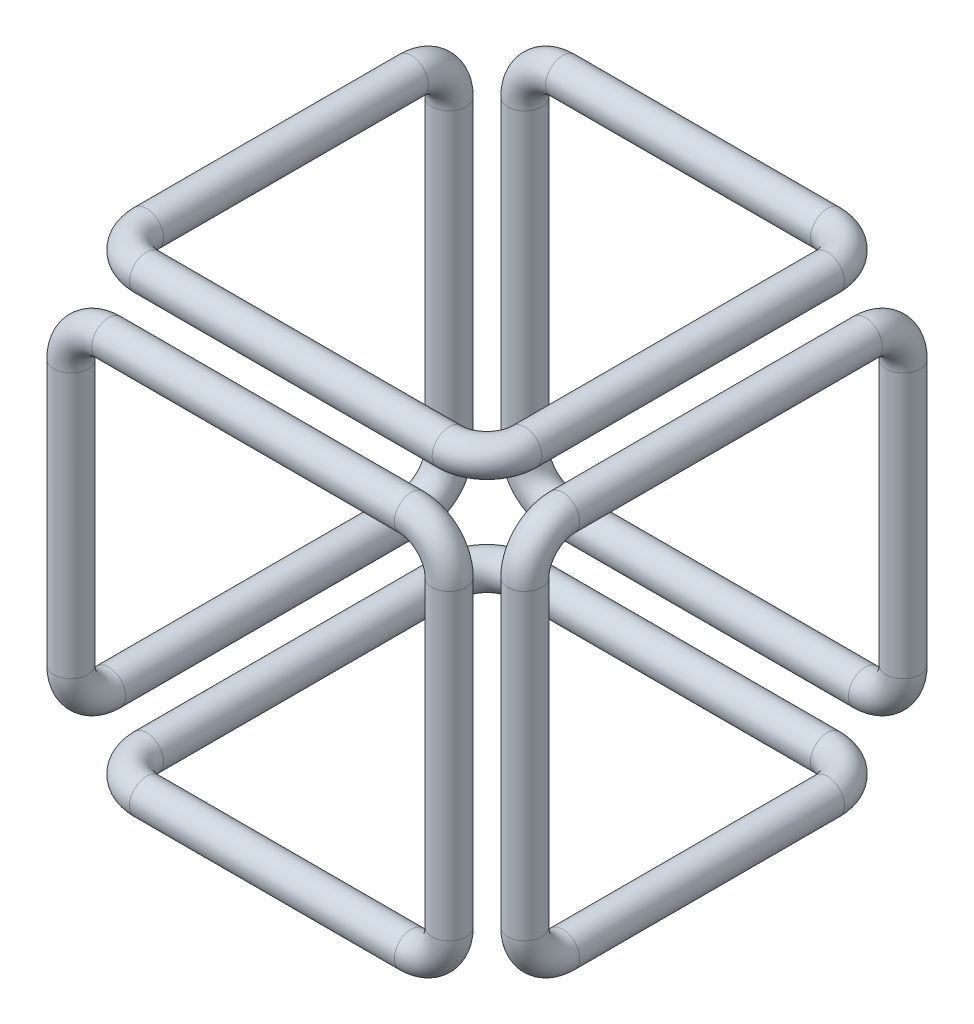
SolidWorks part; units mm, degrees
ref_plane "正面" through (0, 0, 0) normal (0, 0, 1) x (1, 0, 0)
ref_plane "平面" through (0, 0, 0) normal (0, 1, 0) x (1, 0, 0)
ref_plane "右側面" through (0, 0, 0) normal (1, 0, 0) x (0, 0, -1)
sketch3d "3Dｽｹｯﾁ1"
  line L0 (0, 0, 0) -> (100, 0, 0) construction
  line L1 (90, 0, 0) -> (10, 0, 0)
  line L2 (0, 0, 0) -> (0, 79.2192, 0) construction
  line L4 (0, 0, 0) -> (57.5461, 0, 0)
  line L5 (100, 0, 10) -> (100, 0, 80)
  line L6 (100, 10, 90) -> (100, 90, 90)
  line L7 (100, 100, 80) -> (100, 100, 0)
  line L8 (100, 90, -10) -> (100, 20, -10)
  line L9 (90, 10, -10) -> (10, 10, -10)
  line L10 (0, 20, -10) -> (0, 100, -10)
  line L11 (10, 110, -10) -> (80, 110, -10)
  line L12 (90, 110, 0) -> (90, 110, 80)
  line L13 (80, 110, 90) -> (0, 110, 90)
  line L15 (-10, 110, 80) -> (-10, 110, 10)
  line L16 (-10, 100, 0) -> (-10, 20, 0)
  line L17 (-10, 10, 10) -> (-10, 10, 90)
  line L18 (-10, 20, 100) -> (-10, 90, 100)
  line L19 (0, 100, 100) -> (80, 100, 100)
  line L20 (90, 90, 100) -> (90, 10, 100)
  line L22 (80, 0, 100) -> (10, 0, 100)
  line L23 (0, 0, 90) -> (0, 0, 10)
  arc A0 (10, 0, 100) -> (0, 0, 90) centre (10, 0, 90) ccw
  arc A1 (90, 10, 100) -> (80, 0, 100) centre (80, 10, 100) ccw
  arc A2 (80, 100, 100) -> (90, 90, 100) centre (80, 90, 100) ccw
  arc A3 (-10, 90, 100) -> (0, 100, 100) centre (0, 90, 100) ccw
  arc A4 (-10, 10, 90) -> (-10, 20, 100) centre (-10, 20, 90) ccw
  arc A5 (-10, 20, 0) -> (-10, 10, 10) centre (-10, 20, 10) ccw
  arc A6 (0, 110, 90) -> (-10, 110, 80) centre (0, 110, 80) ccw
  arc A7 (90, 110, 80) -> (80, 110, 90) centre (80, 110, 80) ccw
  arc A8 (80, 110, -10) -> (90, 110, 0) centre (80, 110, 0) ccw
  arc A9 (0, 100, -10) -> (10, 110, -10) centre (10, 100, -10) ccw
  arc A10 (-10, 110, 10) -> (-10, 100, 0) centre (-10, 100, 10) ccw
  arc A11 (10, 10, -10) -> (0, 20, -10) centre (10, 20, -10) ccw
  arc A12 (100, 20, -10) -> (90, 10, -10) centre (90, 20, -10) ccw
  arc A13 (100, 100, 0) -> (100, 90, -10) centre (100, 90, 0) ccw
  arc A14 (100, 90, 90) -> (100, 100, 80) centre (100, 90, 80) ccw
  arc A15 (100, 0, 80) -> (100, 10, 90) centre (100, 10, 80) ccw
  arc A16 (100, 0, 10) -> (90, 0, 0) centre (90, 0, 10) ccw
  arc A17 (0, 0, 10) -> (10, 0, 0) centre (10, 0, 10) ccw
  point P17 (-13.1299, 115.1906, 107.347)
  point P26 (2.9806, 104.2992, 101.5385)
  point P28 (0, 0, 100)
  point P29 (10, -10, 90)
  point P32 (90, 0, 100)
  point P33 (80, 10, 90)
  point P36 (90, 100, 100)
  point P37 (80, 90, 90)
  point P40 (-10, 100, 100)
  point P41 (0, 90, 90)
  point P44 (-10, 10, 100)
  point P45 (-20, 20, 90)
  point P48 (-10, 10, 0)
  point P49 (-20, 20, 10)
  point P52 (-10, 110, 90)
  point P53 (0, 100, 80)
  point P56 (90, 110, 90)
  point P57 (80, 100, 80)
  point P60 (90, 110, -10)
  point P61 (80, 100, 0)
  point P64 (0, 110, -10)
  point P65 (10, 100, -20)
  point P68 (-10, 110, 0)
  point P69 (-20, 100, 10)
  point P72 (0, 10, -10)
  point P73 (10, 20, -20)
  point P76 (100, 10, -10)
  point P77 (90, 20, -20)
  point P80 (100, 100, -10)
  point P81 (90, 90, 0)
  point P84 (100, 100, 90)
  point P85 (90, 90, 80)
  point P88 (100, 0, 90)
  point P89 (90, 10, 80)
  point P92 (100, 0, 0)
  point P93 (90, 10, 10)
  point P96 (0, 0, 0)
  point P98 (10, -10, 10)
  dimension "D17" = 10
  dimension "D18" = 10
  dimension "D1" = 100
  dimension "D2" = 90
  dimension "D3" = 100
  dimension "D4" = 90
  dimension "D5" = 100
  dimension "D6" = 90
  dimension "D7" = 100
  dimension "D10" = 90
  dimension "D8" = 100
  dimension "D9" = 100
  dimension "D11" = 100
  dimension "D12" = 90
  dimension "D13" = 100
  dimension "D14" = 90
  dimension "D15" = 100
  dimension "D16" = 100
ref_plane "平面1" through (0, 0, 10) normal (0, 0, 1) x (1, 0, 0)
sketch "ｽｹｯﾁ1" plane through (0, 0, 10) normal (0, 0, 1) x (1, 0, 0)
  circle A0 centre (100, 0) radius 4.5
  dimension "D1" = 9
sweep "ｽｲｰﾌﾟ1" add profiles "ｽｹｯﾁ1" path "3Dｽｹｯﾁ1"
